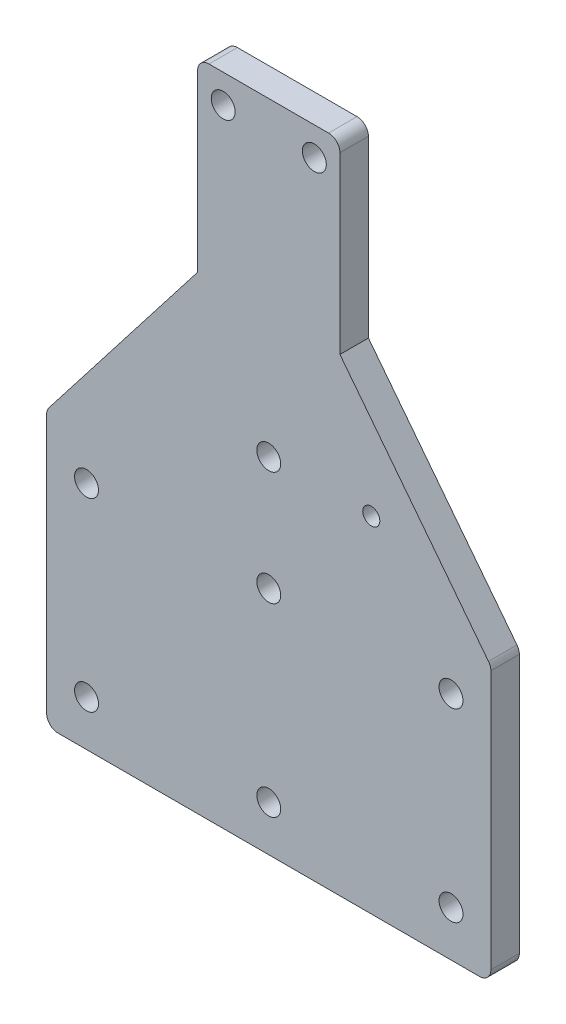
SolidWorks part; units mm, degrees
ref_plane "Front Plane" through (0, 0, 0) normal (0, 0, 1) x (1, 0, 0)
ref_plane "Top Plane" through (0, 0, 0) normal (0, 1, 0) x (1, 0, 0)
ref_plane "Right Plane" through (0, 0, 0) normal (1, 0, 0) x (0, 0, -1)
sketch "Sketch1" plane through (0, 0, 0) normal (0, 0, 1) x (1, 0, 0)
  line L0 (13, 134.575) -> (13, 200) construction
  line L5 (-39, 100.2328) -> (-12.5, 134.4038)
  line L7 (-13, 200) -> (-13, 134.575) construction
  line L8 (-51, 85.575) -> (-51, -100) construction
  line L9 (51, -100) -> (51, 85.575) construction
  line L10 (-75, -100) -> (75, -100)
  line L11 (75, -100) -> (75, 200)
  line L12 (75, 200) -> (-75, 200)
  line L13 (-75, 200) -> (-75, -100)
  line L14 (-75, -100) -> (75, -100) construction
  line L15 (75, -100) -> (75, 200) construction
  line L16 (75, 200) -> (-75, 200) construction
  line L17 (-75, 200) -> (-75, -100) construction
  line L18 (51, 85.575) -> (13, 134.575) construction
  line L19 (-13, 134.575) -> (-51, 85.575) construction
  line L20 (13, 134.575) -> (13, 200) construction
  line L21 (-13, 200) -> (-13, 134.575) construction
  line L22 (-51, 85.575) -> (-51, -100) construction
  line L23 (51, -100) -> (51, 85.575) construction
  line L24 (51, 85.575) -> (13, 134.575) construction
  line L25 (-13, 134.575) -> (-51, 85.575) construction
  line L27 (-39, 100.2328) -> (-39, 52.075)
  line L29 (39, 100.2328) -> (39, 52.075)
  line L30 (-12.5, 145.9889) -> (-13, 145.9889) construction
  line L31 (-32, 110.075) -> (-31.6049, 109.7686) construction
  line L32 (-12.5, 134.4038) -> (-12.5, 167.075)
  line L33 (-12.5, 167.075) -> (12.5, 167.075)
  line L34 (12.5, 167.075) -> (12.5, 134.4038)
  line L35 (12.5, 134.4038) -> (39, 100.2328)
  line L36 (-27.0129, 52.075) -> (27.0129, 52.075)
  line L37 (-39, 52.075) -> (-27.0129, 52.075)
  line L38 (27.0129, 52.075) -> (39, 52.075)
  point P17 (0, 37.075)
  point P24 (0, 167.075)
  dimension "D2" = 15
  dimension "D3" = 0.5
  dimension "D4" = 115
  dimension "D6" = 78
  dimension "D1" = 0
extrude "Boss-Extrude1" add sketch "Sketch1" along normal blind 5
sketch "Sketch2" plane through (0, 0, 0) normal (0, 0, -1) x (-1, 0, 0)
  circle A0 centre (-18, 112.575) radius 2.1 construction
  circle A1 centre (-32, 92.575) radius 1.65 construction
  circle A2 centre (32, 92.575) radius 1.65 construction
  circle A3 centre (-18, 112.575) radius 2.1 construction
  circle A4 centre (-32, 92.575) radius 1.65 construction
  circle A5 centre (32, 92.575) radius 1.65 construction
  circle A6 centre (-8, 162.075) radius 1.65 construction
  circle A7 centre (8, 162.075) radius 1.65 construction
  circle A8 centre (-8, 162.075) radius 1.65 construction
  circle A9 centre (8, 162.075) radius 1.65 construction
  circle A10 centre (-32, 92.575) radius 2.1
  circle A11 centre (32, 92.575) radius 2.1
  circle A12 centre (8, 162.075) radius 2.1
  circle A13 centre (-8, 162.075) radius 2.1
  circle A14 centre (-18, 112.575) radius 1.5
  dimension "D1" = 4.2
  dimension "D2" = 3
extrude "Cut-Extrude1" cut sketch "Sketch2" against normal through all
sketch "Sketch4" plane through (0, 0, 0) normal (0, 0, -1) x (-1, 0, 0)
  line L0 (39, 52.075) -> (-39, 52.075) construction
  circle A0 centre (-32, 60.075) radius 2.1
  circle A1 centre (32, 60.075) radius 2.1
  circle A2 centre (0, 60.075) radius 2.1
  circle A3 centre (0, 112.575) radius 2.1
  circle A4 centre (0, 92.575) radius 2.1
  circle A5 centre (-18, 112.575) radius 1.5 construction
  circle A6 centre (-18, 112.575) radius 1.5 construction
  circle A7 centre (32, 92.575) radius 2.1 construction
  circle A8 centre (-32, 92.575) radius 2.1 construction
  circle A9 centre (32, 92.575) radius 2.1 construction
  circle A10 centre (-32, 92.575) radius 2.1 construction
  dimension "D1" = 4.2
  dimension "D2" = 8
extrude "Cut-Extrude2" cut sketch "Sketch4" against normal through all
fillet "Fillet1" radius 2 6 edges at (39, 52.075, 2.5) (-39, 52.075, 2.5) (-39, 100.2328, 2.5) (39, 100.2328, 2.5) (-12.5, 167.075, 2.5) (12.5, 167.075, 2.5)
